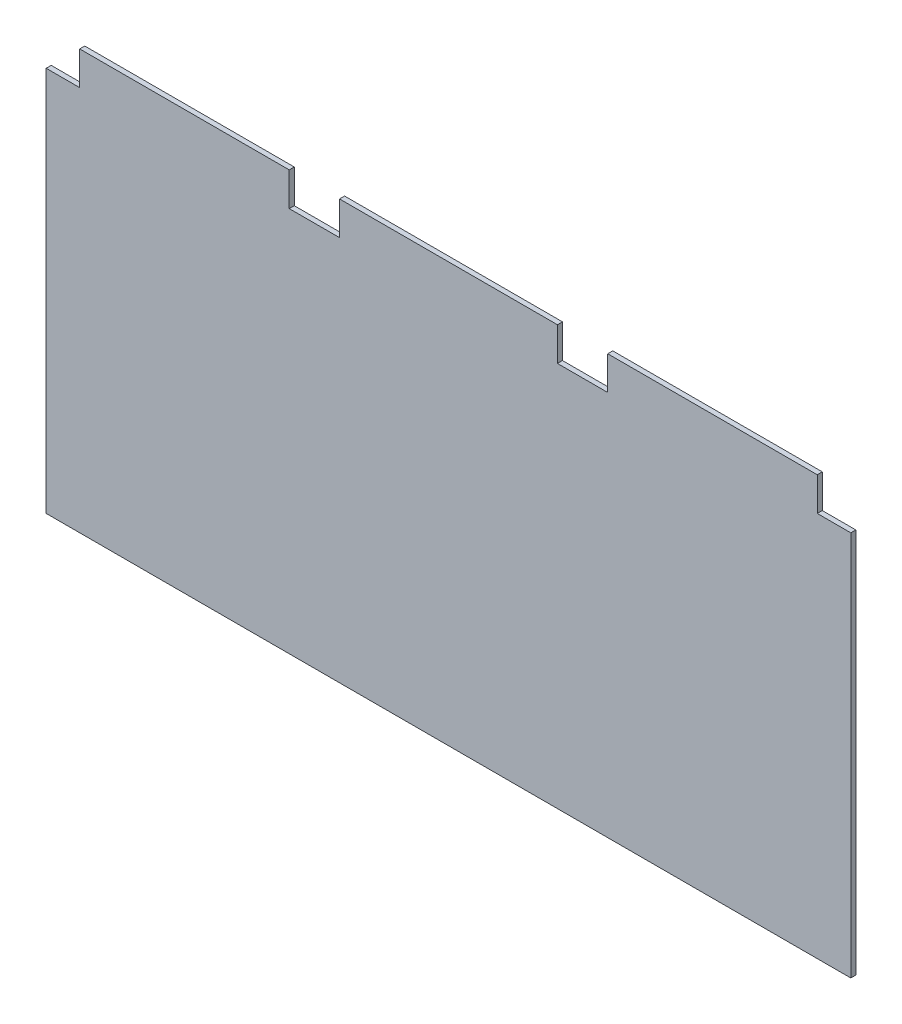
SolidWorks part; units mm, degrees
ref_plane "Alzado" through (0, 0, 0) normal (0, 0, 1) x (1, 0, 0)
ref_plane "Planta" through (0, 0, 0) normal (0, 1, 0) x (1, 0, 0)
ref_plane "Vista lateral" through (0, 0, 0) normal (1, 0, 0) x (0, 0, -1)
sketch "Croquis1" plane through (0, 0, 0) normal (0, 0, 1) x (1, 0, 0)
  line L1 (-250, 130) -> (250, 130)
  line L2 (-250, 130) -> (-250, -130)
  line L3 (-250, -130) -> (250, -130)
  line L4 (250, 130) -> (250, -130)
  line L5 (-250, 130) -> (250, -130) construction
  line L6 (-250, -130) -> (250, 130) construction
  point P0 (0, 0)
  dimension "D1" = 500
  dimension "D2" = 260
extrude "Saliente-Extruir1" add sketch "Croquis1" along normal blind 3
sketch "Croquis2" plane through (0, 0, 3) normal (0, 0, 1) x (1, 0, 0)
  line L0 (0, 0) -> (0, 50000) construction
  line L2 (-95, 130) -> (-65, 130)
  line L3 (-95, 130) -> (-95, 100)
  line L4 (-95, 100) -> (-65, 100)
  line L5 (-65, 130) -> (-65, 100)
  line L6 (-95, 130) -> (-65, 100) construction
  line L7 (-95, 100) -> (-65, 130) construction
  line L14 (250, 130) -> (-250, 130) construction
  line L17 (-250, 130) -> (-220, 130)
  line L18 (-250, 130) -> (-250, 100)
  line L19 (-250, 100) -> (-220, 100)
  line L20 (-220, 130) -> (-220, 100)
  line L21 (-250, 130) -> (-220, 100) construction
  line L22 (-250, 100) -> (-220, 130) construction
  point P7 (-80, 115)
  point P8 (-250, 130)
  point P9 (-55, 130)
  point P20 (-235, 115)
  dimension "D1" = 30
  dimension "D4" = 160
  dimension "D5" = 30
  dimension "D6" = 30
extrude "Cortar-Extruir1" cut sketch "Croquis2" against normal through all
mirror "Simetría1" about plane through (0, 0, 0) normal (1, 0, 0) of "Cortar-Extruir1"
sketch "Croquis3" plane through (0, 0, 3) normal (0, 0, 1) x (1, 0, 0)
  line L0 (0, 0) -> (0, 50000) construction
  line L1 (-250, -130) -> (-240, -130)
  line L2 (-250, -130) -> (-250, 130)
  line L3 (-250, 130) -> (-240, 130)
  line L4 (-240, -130) -> (-240, 130) construction
  line L5 (-250, -130) -> (-240, 130) construction
  line L6 (-250, 130) -> (-240, -130) construction
  line L7 (-240, 120) -> (-240, -130)
  line L8 (0, 130) -> (-240, 130)
  line L9 (0, 130) -> (0, 120)
  line L10 (0, 120) -> (-240, 120)
  line L11 (-240, 130) -> (-240, 120) construction
  line L12 (0, 130) -> (-240, 120) construction
  line L13 (0, 120) -> (-240, 130) construction
  point P4 (-245, 0)
  point P13 (-120, 125)
  dimension "D1" = 10
  dimension "D2" = 10
extrude "Cortar-Extruir2" cut sketch "Croquis3" against normal through all
mirror "Simetría2" about plane through (0, 0, 0) normal (1, 0, 0) of "Cortar-Extruir2"
